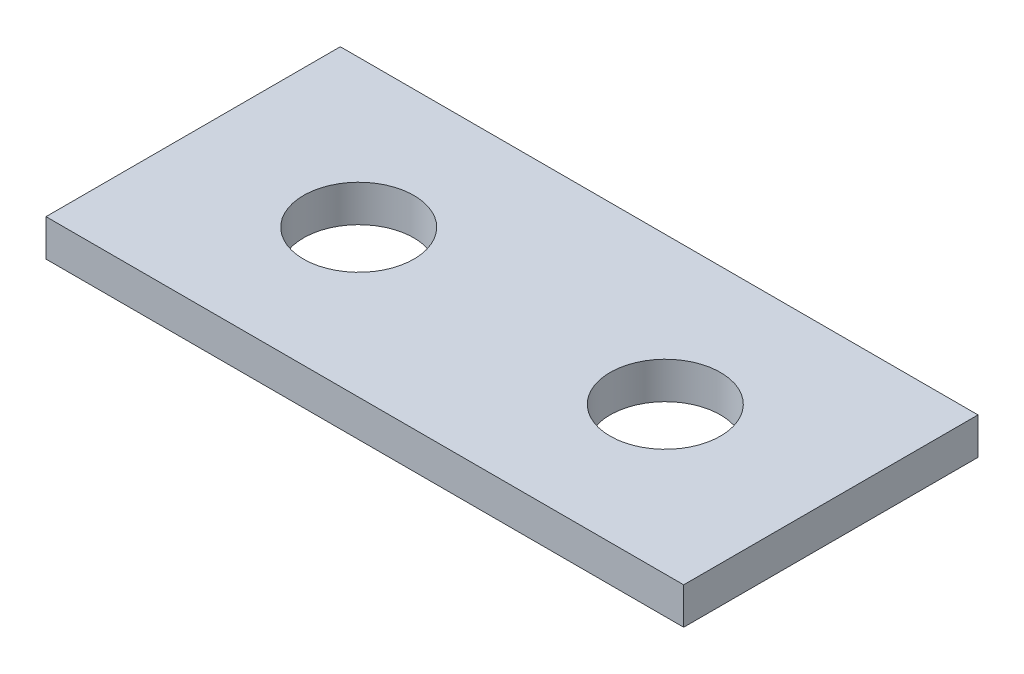
SolidWorks part; units mm, degrees
material "6061-T6 Al"
ref_plane "Front" through (0, 0, 0) normal (0, 0, 1) x (1, 0, 0)
ref_plane "Top" through (0, 0, 0) normal (0, 1, 0) x (1, 0, 0)
ref_plane "Right" through (0, 0, 0) normal (1, 0, 0) x (0, 0, -1)
sketch "Sketch1" plane through (0, 0, 0) normal (0, 1, 0) x (1, 0, 0)
  line L1 (-13, 6) -> (13, 6)
  line L2 (-13, 6) -> (-13, -6)
  line L3 (-13, -6) -> (13, -6)
  line L4 (13, 6) -> (13, -6)
  line L5 (-13, 6) -> (13, -6) construction
  line L6 (-13, -6) -> (13, 6) construction
  point P0 (0, 0)
  dimension "D1" = 26
  dimension "D2" = 12
extrude "Boss-Extrude1" add sketch "Sketch1" along normal blind 1.5
sketch "Sketch2" plane through (0, 1.5, 0) normal (0, 1, 0) x (1, 0, 0)
  line L0 (-13, -6) -> (13, -6) construction
  circle A0 centre (-6.25, 0) radius 2.25
  dimension "D1" = 4.5
  dimension "D2" = 6
  dimension "D3" = 6.25
extrude "Cut-Extrude1" cut sketch "Sketch2" against normal through all
mirror "Mirror1" about plane through (0, 0, 0) normal (1, 0, 0) of "Cut-Extrude1"
